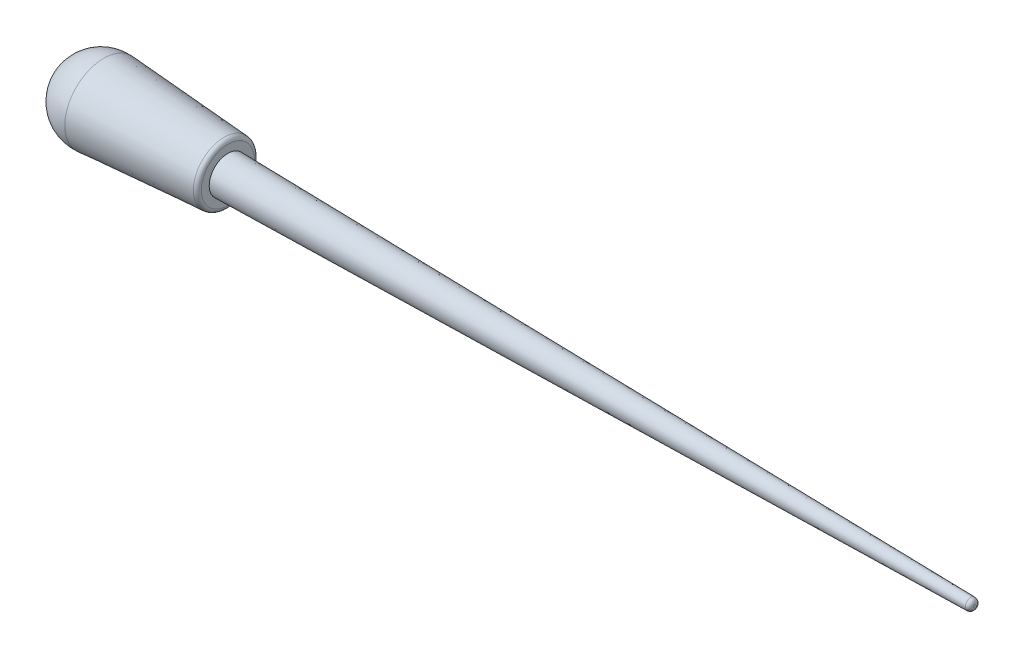
SolidWorks part; units mm, degrees
ref_plane "Front Plane" through (0, 0, 0) normal (0, 0, 1) x (1, 0, 0)
ref_plane "Top Plane" through (0, 0, 0) normal (0, 1, 0) x (1, 0, 0)
ref_plane "Right Plane" through (0, 0, 0) normal (1, 0, 0) x (0, 0, -1)
sketch "Sketch7" plane through (0, 0, 0) normal (0, 1, 0) x (1, 0, 0)
  line L0 (-190.0554, 59.5378) -> (0, 46.5302)
  line L1 (0, 46.5302) -> (0, 0)
  line L4 (-253.8073, 0) -> (0, 0)
  arc A0 (-190.0554, 59.5378) -> (-253.8073, 0) centre (-194.1302, 0) ccw
  dimension "D2" = 190.5
revolve "Revolve4" add sketch "Sketch7" angle 360 about L4
fillet "Fillet1" radius 6.35 1 edges at (0, 0, 46.5302)
sketch "Sketch11" plane through (0, 0, 0) normal (1, 0, 0) x (0, 0, -1)
  circle A0 centre (0, 0) radius 28.575
  dimension "D1" = 57.15
extrude "Boss-Extrude2" add sketch "Sketch11" along normal blind 1143
sketch "Sketch12" plane through (0, 0, 0) normal (0, 0, 1) x (1, 0, 0)
  line L0 (0, 0) -> (1200.348, 0) construction
  line L1 (0, 28.575) -> (1267.8555, 6.1865)
  line L2 (1267.8555, 6.1865) -> (456.3178, 229.961)
  line L3 (456.3178, 229.961) -> (0, 28.575)
  line L4 (1143, 28.575) -> (0, 28.575) construction
revolve "Cut-Revolve1" cut sketch "Sketch12" angle 360 about L0
fillet "Fillet2" radius 6.35 1 edges at (1143, 0, -8.3912)
scale "Scale1" bodies to scale 107 scale about centroid uniform scaling yes scale factor 0.5
scale "Scale2" scale about centroid uniform scaling yes scale factor 0.25
